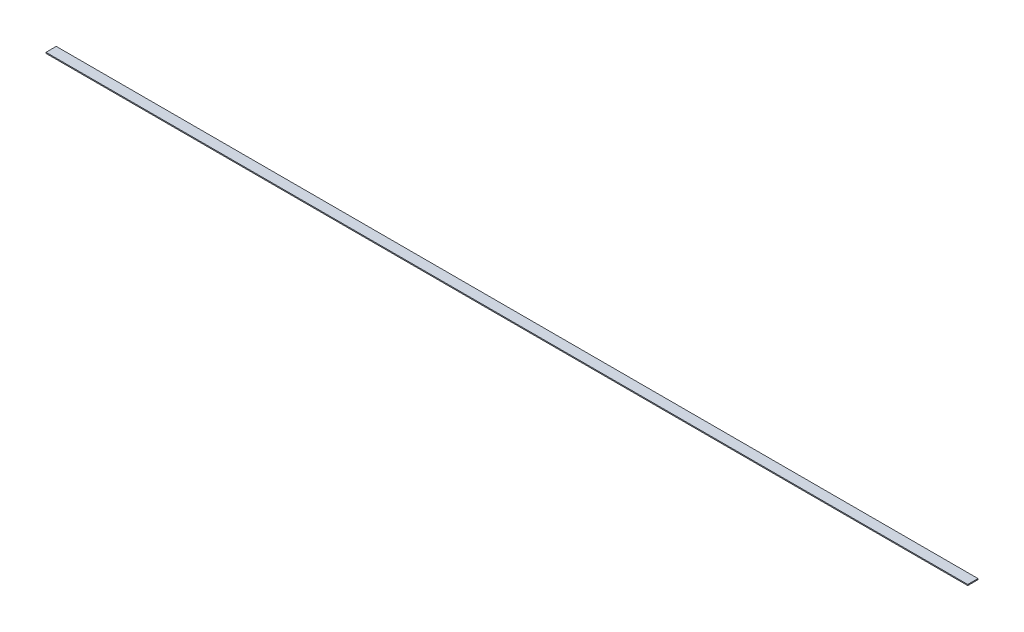
SolidWorks part; units mm, degrees
ref_plane "Front Plane" through (0, 0, 0) normal (0, 0, 1) x (1, 0, 0)
ref_plane "Top Plane" through (0, 0, 0) normal (0, 1, 0) x (1, 0, 0)
ref_plane "Right Plane" through (0, 0, 0) normal (1, 0, 0) x (0, 0, -1)
sketch "Sketch1" plane through (0, 0, 0) normal (0, 1, 0) x (1, 0, 0)
  line L1 (-15.2508, 6.3796) -> (434.7492, 6.3796)
  line L2 (-15.2508, 6.3796) -> (-15.2508, 1.3796)
  line L3 (-15.2508, 1.3796) -> (434.7492, 1.3796)
  line L4 (434.7492, 6.3796) -> (434.7492, 1.3796)
  dimension "D1" = 450
  dimension "D2" = 5
extrude "Boss-Extrude1" add sketch "Sketch1" along normal blind 0.5
